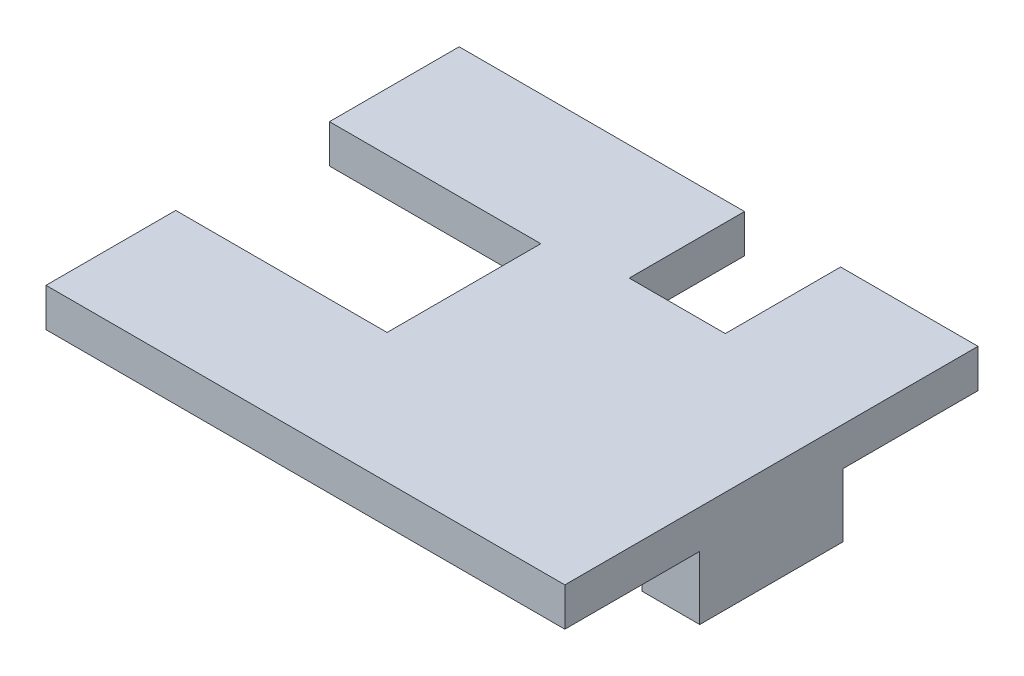
SolidWorks part; units mm, degrees
ref_plane "Спереди" through (0, 0, 0) normal (0, 0, 1) x (1, 0, 0)
ref_plane "Сверху" through (0, 0, 0) normal (0, 1, 0) x (1, 0, 0)
ref_plane "Справа" through (0, 0, 0) normal (1, 0, 0) x (0, 0, -1)
sketch "Sketch1" plane through (0, 0, 0) normal (0, 1, 0) x (1, 0, 0)
  line L0 (-8.0337, 3.2113) -> (-8.0337, 9.9613) construction
  line L1 (-19.0337, 9.9613) -> (-4.1837, 9.9613)
  line L2 (-19.0337, 9.9613) -> (-19.0337, 3.2113)
  line L3 (-19.0337, -11.5387) -> (7.9663, -11.5387)
  line L4 (7.9663, 9.9613) -> (7.9663, -11.5387)
  line L5 (-19.0337, 3.2113) -> (-8.0337, 3.2113)
  line L7 (-19.0337, -4.7887) -> (-8.0337, -4.7887)
  line L8 (-8.0337, 3.2113) -> (-8.0337, -4.7887)
  line L9 (-8.0337, -4.7887) -> (-8.0337, -11.5387) construction
  line L10 (0.8163, 9.9613) -> (7.9663, 9.9613)
  line L12 (-4.1837, 9.9613) -> (-4.1837, 3.9613)
  line L13 (-4.1837, 3.9613) -> (0.8163, 3.9613)
  line L14 (0.8163, 9.9613) -> (0.8163, 3.9613)
  line L15 (-19.0337, -4.7887) -> (-19.0337, -11.5387)
  point P15 (0, 0)
  point P17 (0, 0)
  point P20 (5.572, 0.5809)
  dimension "D1" = 27
  dimension "D2" = 21.5
  dimension "D3" = 8
  dimension "D4" = 11
  dimension "D5" = 6
  dimension "D6" = 5
  dimension "D7" = 7.15
extrude "Boss-Extrude1" add sketch "Sketch1" along normal blind 2
sketch "Sketch2" plane through (0, 0, 0) normal (0, -1, 0) x (1, 0, 0)
  line L0 (7.9663, 11.5387) -> (7.9663, -9.9613) construction
  line L1 (7.9663, 4.5187) -> (4.9663, 4.5187)
  line L2 (7.9663, 4.5187) -> (7.9663, -2.9413)
  line L3 (7.9663, -2.9413) -> (4.9663, -2.9413)
  line L4 (4.9663, 4.5187) -> (4.9663, -2.9413)
  line L5 (6.4663, 11.5387) -> (6.4663, 4.5187) construction
  line L6 (-19.0337, 11.5387) -> (7.9663, 11.5387) construction
  line L7 (6.4663, -2.9413) -> (6.4663, -9.9613) construction
  line L8 (7.9663, -9.9613) -> (0.8163, -9.9613) construction
  point P14 (6.4663, 11.5387)
  dimension "D1" = 7.46
  dimension "D2" = 3
extrude "Boss-Extrude2" add sketch "Sketch2" along normal blind 3.3
